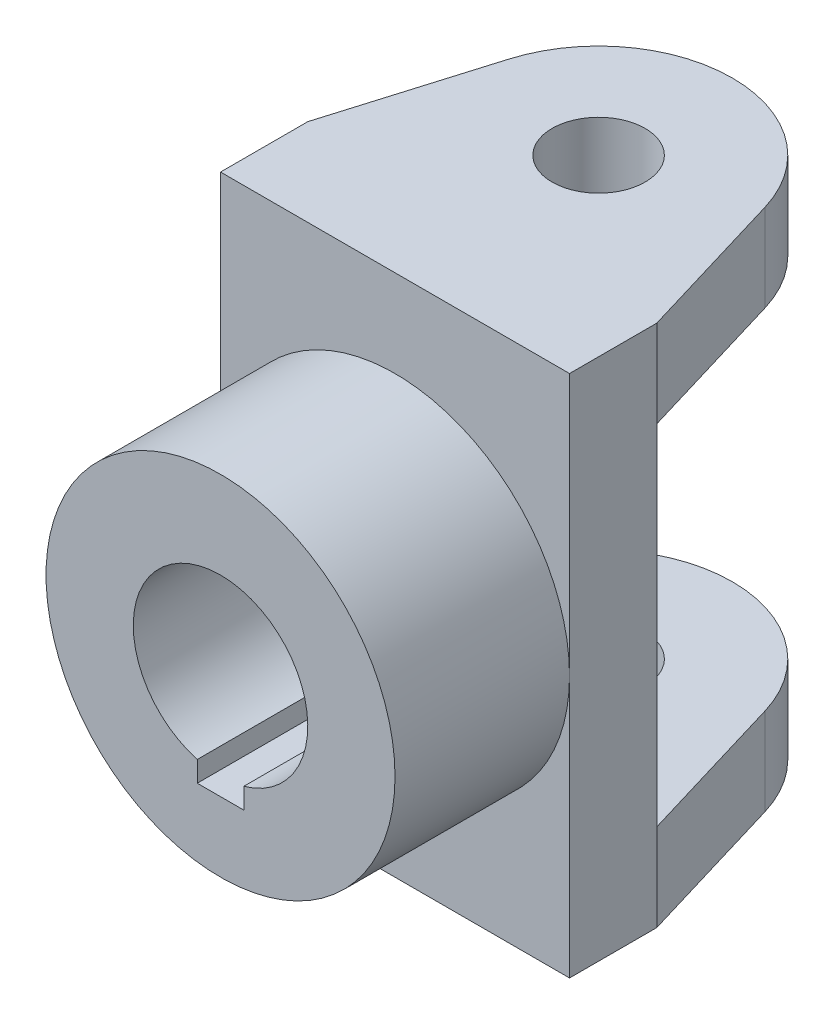
SolidWorks part; units mm, degrees
ref_plane "Front Plane" through (0, 0, 0) normal (0, 0, 1) x (1, 0, 0)
ref_plane "Top Plane" through (0, 0, 0) normal (0, 1, 0) x (1, 0, 0)
ref_plane "Right Plane" through (0, 0, 0) normal (1, 0, 0) x (0, 0, -1)
sketch "Sketch1" plane through (0, 0, 0) normal (0, 0, 1) x (1, 0, 0)
  line L1 (-30, 45) -> (30, 45)
  line L2 (-30, 45) -> (-30, -45)
  line L3 (-30, -45) -> (30, -45)
  line L4 (30, 45) -> (30, -45)
  line L5 (-30, 45) -> (30, -45) construction
  line L6 (-30, -45) -> (30, 45) construction
  point P0 (0, 0)
  dimension "D1" = 60
  dimension "D2" = 90
extrude "Boss-Extrude1" add sketch "Sketch1" along normal blind 15
sketch "Sketch2" plane through (0, 0, 15) normal (0, 0, 1) x (1, 0, 0)
  line L0 (-4, -14.4568) -> (-4, -18)
  line L3 (-4, -18) -> (4, -18)
  line L4 (4, -14.4568) -> (4, -18)
  circle A0 centre (0, 0) radius 30
  arc A1 (4, -14.4568) -> (-4, -14.4568) centre (0, 0) ccw
  dimension "D1" = 60
  dimension "D2" = 30
extrude "Boss-Extrude2" add sketch "Sketch2" along normal blind 30
sketch "Sketch3" plane through (0, 45, 0) normal (0, 1, 0) x (1, 0, 0)
  line L0 (-30, -15) -> (30, -15) construction
  line L1 (-30, 0) -> (30, 0)
  line L2 (-30, 0) -> (-22.0329, 26.5993)
  line L3 (30, 0) -> (22.0329, 26.5993)
  circle A1 centre (0, 20) radius 8
  arc A2 (22.0329, 26.5993) -> (-22.0329, 26.5993) centre (0, 20) ccw
  point P5 (0, -15)
  point P10 (0, 0)
  dimension "D2" = 16
  dimension "D3" = 35
extrude "Boss-Extrude3" add sketch "Sketch3" against normal blind 15
mirror "Mirror1" about plane through (0, 0, 0) normal (0, 1, 0) of "Boss-Extrude3"
